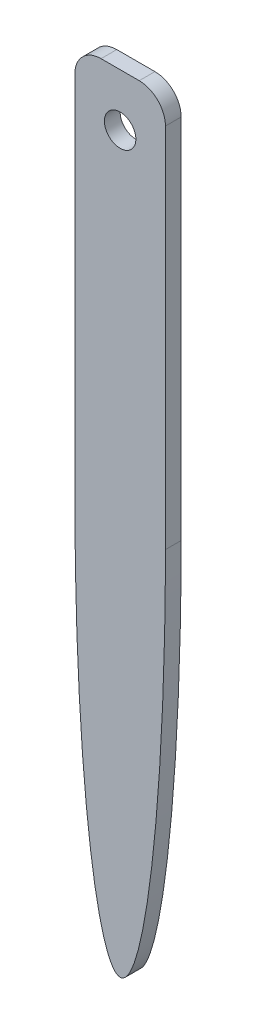
SolidWorks part; units mm, degrees
ref_plane "前视基准面" through (0, 0, 0) normal (0, 0, 1) x (1, 0, 0)
ref_plane "上视基准面" through (0, 0, 0) normal (0, 1, 0) x (1, 0, 0)
ref_plane "右视基准面" through (0, 0, 0) normal (1, 0, 0) x (0, 0, -1)
sketch "草图2" plane through (0, 0, 0) normal (0, 0, 1) x (1, 0, 0)
  line L1 (-3.6417, 75) -> (3.6417, 75)
  line L2 (-8.6417, 70) -> (-8.6417, 0)
  line L4 (8.6417, 70) -> (8.6417, 0)
  line L5 (-8.6417, 75) -> (6.1106, -53.033) construction
  line L6 (-6.1106, -53.033) -> (8.6417, 75) construction
  circle A0 centre (0, 65) radius 3
  arc A1 (3.6417, 75) -> (8.6417, 70) centre (3.6417, 70) cw
  arc A2 (-3.6417, 75) -> (-8.6417, 70) centre (-3.6417, 70) ccw
  ellipse E0 centre (0, 0) end of major axis (0, -75) minor radius 8.6417 (-8.6417, 0) -> (8.6417, 0) ccw
  point P0 (0, 0)
  dimension "D1" = 6
  dimension "D3" = 10
  dimension "D4" = 5
extrude "凸台-拉伸1" add sketch "草图2" along normal blind 3
